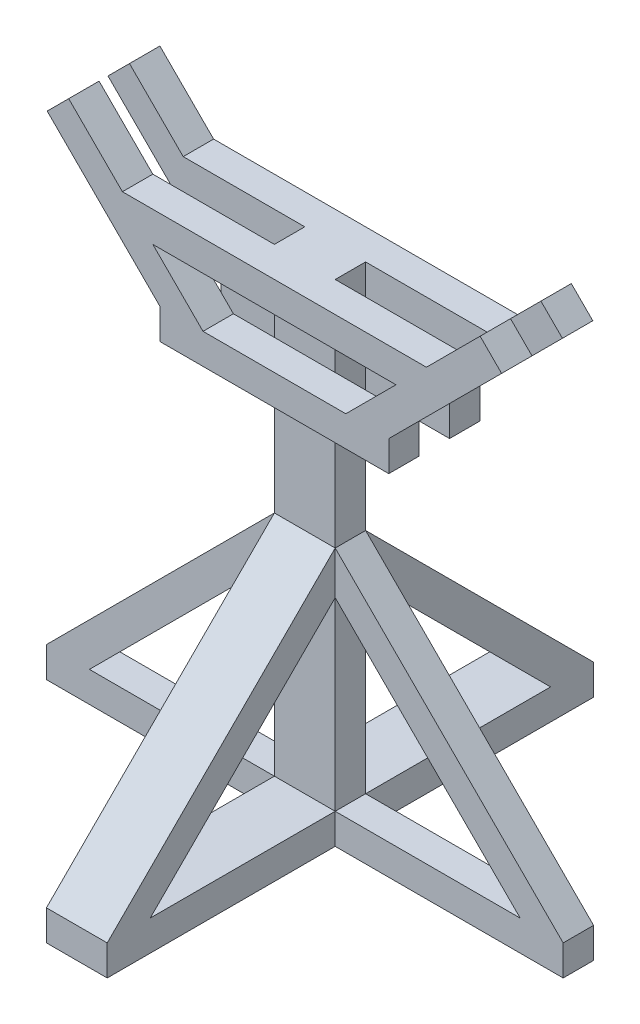
SolidWorks part; units mm, degrees
ref_plane "前视基准面" through (0, 0, 0) normal (0, 0, 1) x (1, 0, 0)
ref_plane "上视基准面" through (0, 0, 0) normal (0, 1, 0) x (1, 0, 0)
ref_plane "右视基准面" through (0, 0, 0) normal (1, 0, 0) x (0, 0, -1)
sketch "草图1" plane through (0, 0, 0) normal (0, 1, 0) x (1, 0, 0)
  line L1 (0, 0) -> (80, 0)
  line L2 (0, 0) -> (0, -40)
  line L3 (0, -40) -> (80, -40)
  line L4 (80, 0) -> (80, -40)
  dimension "D1" = 40
  dimension "D2" = 80
extrude "凸台-拉伸1" add sketch "草图1" along normal blind 500
sketch "草图2" plane through (0, 0, 40) normal (0, 0, 1) x (1, 0, 0)
  line L0 (40, 500) -> (40, 0) construction
  line L1 (-160, 500) -> (240, 500)
  line L2 (-160, 500) -> (-160, 460)
  line L3 (-160, 460) -> (240, 460)
  line L4 (240, 500) -> (240, 460)
  line L5 (0, 500) -> (80, 500) construction
  line L6 (0, 0) -> (80, 0) construction
  dimension "D1" = 40
  dimension "D2" = 200
  dimension "D3" = 200
extrude "凸台-拉伸2" add sketch "草图2" along normal blind 40
sketch "草图3" plane through (0, 0, 0) normal (0, 0, -1) x (-1, 0, 0)
  line L0 (-40, 500) -> (-40, 0) construction
  line L1 (-80, 500) -> (0, 500) construction
  line L2 (-80, 0) -> (0, 0) construction
  line L8 (-240, 500) -> (160, 500)
  line L9 (-240, 500) -> (-240, 460)
  line L10 (-240, 460) -> (160, 460)
  line L11 (160, 500) -> (160, 460)
  point P10 (0, 0)
  point P11 (0, 0)
  dimension "D1" = 200
  dimension "D2" = 200
  dimension "D3" = 40
extrude "凸台-拉伸3" add sketch "草图3" along normal blind 40
sketch "草图4" plane through (0, 0, 80) normal (0, 0, 1) x (1, 0, 0)
  line L0 (-160, 500) -> (-120, 460)
  line L1 (240, 500) -> (200, 460)
  line L3 (-160, 460) -> (240, 460) construction
  line L4 (-160, 500) -> (-160, 460)
  line L5 (-160, 460) -> (240, 460)
  line L6 (240, 460) -> (240, 500)
  line L7 (240, 500) -> (-160, 500)
  line L8 (-160, 500) -> (-160, 460)
  line L9 (-160, 460) -> (-120, 460)
  line L10 (240, 460) -> (240, 500)
  line L12 (200, 460) -> (240, 460)
  dimension "D2" = 45
  dimension "D3" = 45
  dimension "D1" = 0
extrude "切除-拉伸1" cut sketch "草图4" against normal through all
sketch "草图5" plane through (-130, 130, 0) normal (0.7071, -0.7071, 0) x (0, 0, -1)
  line L1 (-80, 523.259) -> (-40, 523.259)
  line L2 (-80, 523.259) -> (-80, 373.259)
  line L3 (-80, 373.259) -> (-40, 373.259)
  line L4 (-40, 523.259) -> (-40, 373.259)
  dimension "D1" = 40
  dimension "D2" = 150
extrude "凸台-拉伸4" add sketch "草图5" along normal blind 40
sketch "草图6" plane through (370, 370, 0) normal (0.7071, 0.7071, 0) x (0, 0, -1)
  line L4 (-40, 183.8478) -> (-80, 183.8478)
  line L5 (-80, 183.8478) -> (-80, 143.8478)
  line L6 (-80, 143.8478) -> (-40, 143.8478)
  line L7 (-40, 143.8478) -> (-40, 183.8478)
  line L8 (-40, 183.8478) -> (-80, 183.8478)
  line L9 (-80, 183.8478) -> (-80, 143.8478)
  line L10 (-80, 143.8478) -> (-40, 143.8478)
  line L11 (-40, 143.8478) -> (-40, 183.8478)
  dimension "D1" = 0
extrude "凸台-拉伸5" add sketch "草图6" along normal blind 100
sketch "草图7" plane through (-130, 130, 0) normal (0.7071, -0.7071, 0) x (0, 0, -1)
  line L1 (0, 523.259) -> (40, 523.259)
  line L2 (0, 523.259) -> (0, 373.259)
  line L3 (0, 373.259) -> (40, 373.259)
  line L4 (40, 523.259) -> (40, 373.259)
  dimension "D1" = 40
  dimension "D2" = 150
extrude "凸台-拉伸6" add sketch "草图7" along normal blind 40
sketch "草图8" plane through (370, 370, 0) normal (0.7071, 0.7071, 0) x (0, 0, -1)
  line L4 (40, 183.8478) -> (0, 183.8478)
  line L5 (0, 183.8478) -> (0, 143.8478)
  line L6 (0, 143.8478) -> (40, 143.8478)
  line L7 (40, 143.8478) -> (40, 183.8478)
  line L8 (40, 183.8478) -> (0, 183.8478)
  line L9 (0, 183.8478) -> (0, 143.8478)
  line L10 (0, 143.8478) -> (40, 143.8478)
  line L11 (40, 143.8478) -> (40, 183.8478)
  dimension "D1" = 0
extrude "凸台-拉伸7" add sketch "草图8" along normal blind 100
sketch "草图9" plane through (170, 170, 0) normal (-0.7071, -0.7071, 0) x (0, 0, 1)
  line L1 (-40, 466.6905) -> (0, 466.6905)
  line L2 (-40, 466.6905) -> (-40, 316.6905)
  line L3 (-40, 316.6905) -> (0, 316.6905)
  line L4 (0, 466.6905) -> (0, 316.6905)
  line L5 (40, 466.6905) -> (80, 466.6905)
  line L6 (40, 466.6905) -> (40, 316.6905)
  line L7 (40, 316.6905) -> (80, 316.6905)
  line L8 (80, 466.6905) -> (80, 316.6905)
  dimension "D1" = 40
  dimension "D2" = 40
  dimension "D3" = 150
  dimension "D4" = 150
extrude "凸台-拉伸8" add sketch "草图9" along normal blind 40
sketch "草图10" plane through (-330, 330, 0) normal (-0.7071, 0.7071, 0) x (0, 0, 1)
  line L4 (0, 240.4163) -> (-40, 240.4163)
  line L5 (-40, 240.4163) -> (-40, 200.4163)
  line L6 (-40, 200.4163) -> (0, 200.4163)
  line L7 (0, 200.4163) -> (0, 240.4163)
  line L8 (0, 240.4163) -> (-40, 240.4163)
  line L9 (-40, 240.4163) -> (-40, 200.4163)
  line L10 (-40, 200.4163) -> (0, 200.4163)
  line L11 (0, 200.4163) -> (0, 240.4163)
  line L12 (80, 240.4163) -> (40, 240.4163)
  line L13 (40, 240.4163) -> (40, 200.4163)
  line L14 (40, 200.4163) -> (80, 200.4163)
  line L15 (80, 200.4163) -> (80, 240.4163)
  line L16 (80, 240.4163) -> (40, 240.4163)
  line L17 (40, 240.4163) -> (40, 200.4163)
  line L18 (40, 200.4163) -> (80, 200.4163)
  line L19 (80, 200.4163) -> (80, 240.4163)
  dimension "D1" = 0
  dimension "D2" = 0
extrude "凸台-拉伸9" add sketch "草图10" along normal blind 100
sketch "草图12" plane through (0, 0, 80) normal (0, 0, 1) x (1, 0, 0)
  line L0 (-53.934, 393.934) -> (-110.5025, 393.934)
  line L1 (133.934, 393.934) -> (190.5025, 393.934)
  line L12 (240, 500) -> (-160, 500)
  line L13 (-160, 500) -> (-230.7107, 570.7107)
  line L14 (-230.7107, 570.7107) -> (-258.9949, 542.4264)
  line L15 (-258.9949, 542.4264) -> (-82.2183, 365.6497)
  line L16 (-82.2183, 365.6497) -> (-53.934, 393.934)
  line L17 (-53.934, 393.934) -> (-120, 460)
  line L18 (-120, 460) -> (200, 460)
  line L19 (200, 460) -> (133.934, 393.934)
  line L20 (133.934, 393.934) -> (162.2183, 365.6497)
  line L21 (162.2183, 365.6497) -> (338.9949, 542.4264)
  line L22 (338.9949, 542.4264) -> (310.7107, 570.7107)
  line L23 (310.7107, 570.7107) -> (240, 500)
  line L27 (-110.5025, 393.934) -> (-82.2183, 365.6497)
  line L28 (-82.2183, 365.6497) -> (-53.934, 393.934)
  line L32 (133.934, 393.934) -> (162.2183, 365.6497)
  line L33 (162.2183, 365.6497) -> (190.5025, 393.934)
  line L34 (338.9949, 542.4264) -> (310.7107, 570.7107)
  line M17 (-258.9949, 542.4264) -> (-82.2183, 365.6497)
  line M18 (-82.2183, 365.6497) -> (-53.934, 393.934)
  dimension "D2" = 45
  dimension "D1" = 0
extrude "切除-拉伸2" cut sketch "草图12" against normal through all contours L0 M18 M17 | L32 L33 L1
sketch "草图13" plane through (0, 393.934, 0) normal (0, -1, 0) x (1, 0, 0)
  line L1 (-110.5025, 80) -> (190.5025, 80)
  line L2 (-110.5025, 80) -> (-110.5025, 40)
  line L3 (-110.5025, 40) -> (190.5025, 40)
  line L4 (190.5025, 80) -> (190.5025, 40)
  line L5 (-110.5025, 0) -> (190.5025, 0)
  line L6 (-110.5025, 0) -> (-110.5025, -40)
  line L7 (-110.5025, -40) -> (190.5025, -40)
  line L8 (190.5025, 0) -> (190.5025, -40)
extrude "凸台-拉伸10" add sketch "草图13" along normal blind 40
sketch "草图14" plane through (0, 353.934, 0) normal (0, -1, 0) x (-1, 0, 0)
  line L0 (110.5025, -40) -> (0, -40) construction
  line L1 (110.5025, -80) -> (70.5025, -80)
  line L2 (110.5025, -80) -> (110.5025, -40)
  line L3 (110.5025, -40) -> (70.5025, -40)
  line L4 (70.5025, -80) -> (70.5025, -40)
  line L5 (110.5025, 40) -> (-190.5025, 40) construction
  line L6 (110.5025, 0) -> (70.5025, 0)
  line L7 (110.5025, 0) -> (110.5025, 40)
  line L8 (110.5025, 40) -> (70.5025, 40)
  line L9 (70.5025, 0) -> (70.5025, 40)
  line L10 (-80, -40) -> (-190.5025, -40) construction
  line L11 (-190.5025, -80) -> (-150.5025, -80)
  line L12 (-190.5025, -80) -> (-190.5025, -40)
  line L13 (-190.5025, -40) -> (-150.5025, -40)
  line L14 (-150.5025, -80) -> (-150.5025, -40)
  line L16 (-190.5025, 0) -> (-150.5025, 0)
  line L17 (-190.5025, 0) -> (-190.5025, 40)
  line L18 (-190.5025, 40) -> (-150.5025, 40)
  line L19 (-150.5025, 0) -> (-150.5025, 40)
  dimension "D1" = 40
  dimension "D2" = 40
  dimension "D3" = 40
  dimension "D4" = 40
extrude "凸台-拉伸11" add sketch "草图14" along normal blind 500
sketch "草图15" plane through (0, 0, 0) normal (0, -1, 0) x (1, 0, 0)
  line L4 (0, 40) -> (0, 0)
  line L5 (0, 0) -> (80, 0)
  line L6 (80, 0) -> (80, 40)
  line L7 (80, 40) -> (0, 40)
  line L8 (0, 40) -> (0, 0)
  line L9 (0, 0) -> (80, 0)
  line L10 (80, 0) -> (80, 40)
  line L11 (80, 40) -> (0, 40)
  dimension "D1" = 0
extrude "凸台-拉伸12" add sketch "草图15" along normal up to surface (146.066 mm away) up to face at (170.5025, -146.066, 60)
sketch "草图17" plane through (-70.5025, 0, 0) normal (1, 0, 0) x (0, 0, -1)
  line L0 (-80, -146.066) -> (-80, 353.934) construction
  line L1 (-40, -146.066) -> (-80, -146.066)
  line L2 (-40, -146.066) -> (-40, -106.066)
  line L3 (-40, -106.066) -> (-80, -106.066)
  line L4 (-80, -146.066) -> (-80, -106.066)
  line L5 (0, -146.066) -> (0, 353.934) construction
  line L6 (40, -146.066) -> (0, -146.066)
  line L7 (40, -146.066) -> (40, -106.066)
  line L8 (40, -106.066) -> (0, -106.066)
  line L9 (0, -146.066) -> (0, -106.066)
  dimension "D1" = 40
  dimension "D2" = 40
extrude "凸台-拉伸13" add sketch "草图17" along normal up to next
sketch "草图18" plane through (0, -146.066, 0) normal (0, -1, 0) x (1, 0, 0)
  line L12 (-110.5025, 80) -> (-110.5025, 40)
  line L13 (-110.5025, 40) -> (0, 40)
  line L14 (0, 40) -> (0, 0)
  line L15 (0, 0) -> (-110.5025, 0)
  line L16 (-110.5025, 0) -> (-110.5025, -40)
  line L17 (-110.5025, -40) -> (190.5025, -40)
  line L18 (190.5025, -40) -> (190.5025, 0)
  line L19 (190.5025, 0) -> (80, 0)
  line L20 (80, 0) -> (80, 40)
  line L21 (80, 40) -> (190.5025, 40)
  line L22 (190.5025, 40) -> (190.5025, 80)
  line L23 (190.5025, 80) -> (-110.5025, 80)
  line L24 (-110.5025, 80) -> (-110.5025, 40)
  line L25 (-110.5025, 40) -> (0, 40)
  line L26 (0, 40) -> (0, 0)
  line L27 (0, 0) -> (-110.5025, 0)
  line L28 (-110.5025, 0) -> (-110.5025, -40)
  line L29 (-110.5025, -40) -> (190.5025, -40)
  line L30 (190.5025, -40) -> (190.5025, 0)
  line L31 (190.5025, 0) -> (80, 0)
  line L32 (80, 0) -> (80, 40)
  line L33 (80, 40) -> (190.5025, 40)
  line L34 (190.5025, 40) -> (190.5025, 80)
  line L35 (190.5025, 80) -> (-110.5025, 80)
  dimension "D1" = 0
extrude "切除-拉伸3" cut sketch "草图18" against normal blind 500
sketch "草图19" plane through (0, 353.934, 0) normal (0, -1, 0) x (1, 0, 0)
  line L0 (0, 40) -> (80, 40)
  line L1 (0, 0) -> (80, 0)
  line L12 (80, 40) -> (190.5025, 40)
  line L13 (190.5025, 40) -> (190.5025, 80)
  line L14 (190.5025, 80) -> (-110.5025, 80)
  line L15 (-110.5025, 80) -> (-110.5025, 40)
  line L16 (-110.5025, 40) -> (0, 40)
  line L17 (0, 40) -> (0, 0)
  line L18 (0, 0) -> (-110.5025, 0)
  line L19 (-110.5025, 0) -> (-110.5025, -40)
  line L20 (-110.5025, -40) -> (190.5025, -40)
  line L21 (190.5025, -40) -> (190.5025, 0)
  line L22 (190.5025, 0) -> (80, 0)
  line L23 (80, 0) -> (80, 40)
  line L29 (0, 40) -> (0, 0)
  line L35 (80, 0) -> (80, 40)
  dimension "D1" = 0
extrude "凸台-拉伸14" add sketch "草图19" along normal blind 500
sketch "草图20" plane through (0, 0, 40) normal (0, 0, 1) x (1, 0, 0)
  line L0 (0, -146.066) -> (0, 353.934) construction
  line L1 (80, -146.066) -> (0, -146.066)
  line L2 (80, -146.066) -> (80, -106.066)
  line L3 (80, -106.066) -> (0, -106.066)
  line L4 (0, -146.066) -> (0, -106.066)
  dimension "D1" = 40
extrude "凸台-拉伸15" add sketch "草图20" along normal blind 300
sketch "草图21" plane through (80, 0, 0) normal (1, 0, 0) x (0, 0, -1)
  line L1 (0, -146.066) -> (-40, -146.066)
  line L2 (0, -146.066) -> (0, -106.066)
  line L3 (0, -106.066) -> (-40, -106.066)
  line L4 (-40, -146.066) -> (-40, -106.066)
extrude "凸台-拉伸16" add sketch "草图21" along normal blind 300
sketch "草图22" plane through (0, 0, 0) normal (0, 0, -1) x (-1, 0, 0)
  line L1 (0, -146.066) -> (-80, -146.066)
  line L2 (0, -146.066) -> (0, -106.066)
  line L3 (0, -106.066) -> (-80, -106.066)
  line L4 (-80, -146.066) -> (-80, -106.066)
extrude "凸台-拉伸17" add sketch "草图22" along normal blind 300
sketch "草图23" plane through (0, 0, 0) normal (-1, 0, 0) x (0, 0, 1)
  line L0 (340, -146.066) -> (-300, -146.066) construction
  line L1 (0, -106.066) -> (40, -106.066)
  line L2 (0, -106.066) -> (0, -146.066)
  line L3 (0, -146.066) -> (40, -146.066)
  line L4 (40, -106.066) -> (40, -146.066)
  dimension "D1" = 40
extrude "凸台-拉伸18" add sketch "草图23" along normal blind 300
sketch "草图24" plane through (0, 0, 40) normal (0, 0, 1) x (1, 0, 0)
  line L0 (-243.4315, -106.066) -> (0, 137.3654)
  line L1 (0, -106.066) -> (0, 353.934) construction
  line L2 (-300, -106.066) -> (0, -106.066) construction
  line L3 (0, 193.934) -> (-300, -106.066)
  line L5 (-300, -106.066) -> (-243.4315, -106.066)
  line L6 (0, 193.934) -> (0, 137.3654)
  dimension "D1" = 45
  dimension "D2" = 40
extrude "凸台-拉伸19" add sketch "草图24" against normal blind 40
sketch "草图25" plane through (0, 0, 40) normal (0, 0, 1) x (1, 0, 0)
  line L0 (380, -106.066) -> (80, 193.934)
  line L1 (80, -106.066) -> (80, 353.934) construction
  line L2 (323.4315, -106.066) -> (80, 137.3654)
  line L3 (380, -106.066) -> (80, -106.066) construction
  line L4 (80, 193.934) -> (80, 137.3654)
  line L5 (323.4315, -106.066) -> (380, -106.066)
  dimension "D1" = 45
  dimension "D2" = 40
extrude "凸台-拉伸20" add sketch "草图25" against normal blind 40
sketch "草图26" plane through (0, 0, 0) normal (-1, 0, 0) x (0, 0, 1)
  line L0 (-300, -106.066) -> (0, 193.934)
  line L1 (-243.4315, -106.066) -> (0, 137.3654)
  line L2 (-300, -106.066) -> (0, -106.066) construction
  line L3 (0, -106.066) -> (0, 137.3654) construction
  line L4 (-300, -106.066) -> (-243.4315, -106.066)
  line L5 (0, 193.934) -> (0, 137.3654)
  dimension "D1" = 45
  dimension "D2" = 40
extrude "凸台-拉伸21" add sketch "草图26" against normal blind 80
sketch "草图27" plane through (0, 0, 0) normal (-1, 0, 0) x (0, 0, 1)
  line L0 (340, -106.066) -> (40, 193.934)
  line L1 (40, -106.066) -> (40, 137.3654) construction
  line L2 (283.4315, -106.066) -> (40, 137.3654)
  line L3 (340, -106.066) -> (40, -106.066) construction
  line L4 (40, 193.934) -> (40, 137.3654)
  line L5 (283.4315, -106.066) -> (340, -106.066)
  dimension "D1" = 45
  dimension "D2" = 40
extrude "凸台-拉伸22" add sketch "草图27" against normal blind 80
